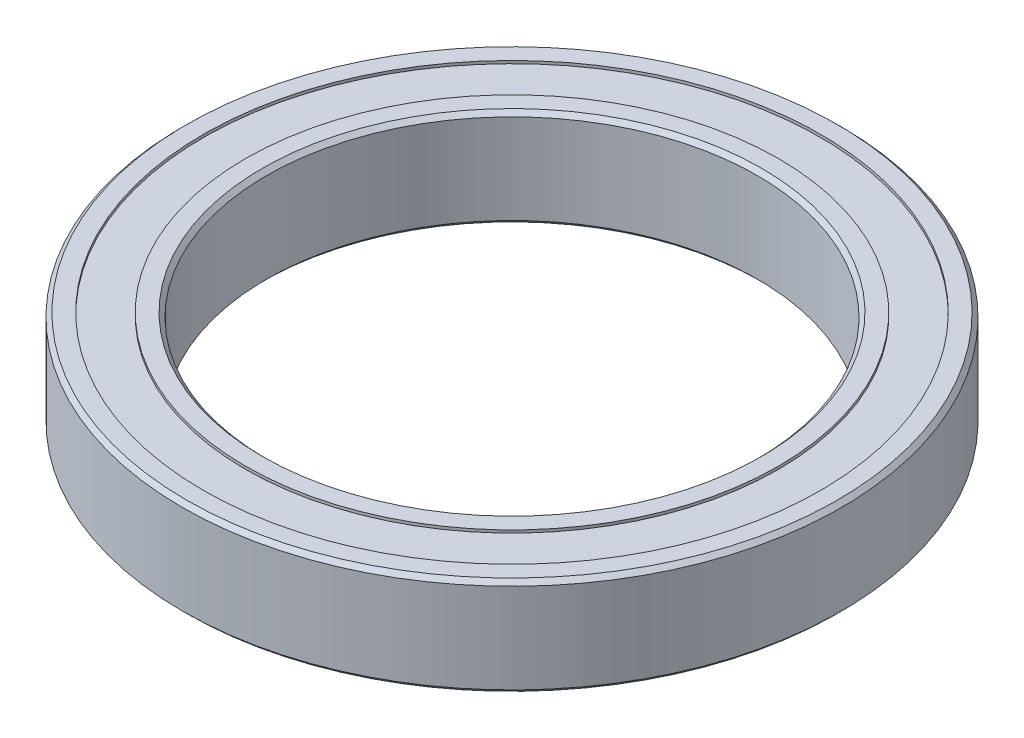
SolidWorks part; units mm, degrees
ref_plane "Front Plane" through (0, 0, 0) normal (0, 0, 1) x (1, 0, 0)
ref_plane "Top Plane" through (0, 0, 0) normal (0, 1, 0) x (1, 0, 0)
ref_plane "Right Plane" through (0, 0, 0) normal (1, 0, 0) x (0, 0, -1)
sketch "Sketch1" plane through (0, 0, 0) normal (0, 1, 0) x (1, 0, 0)
  circle A0 centre (0, 0) radius 17.5
  circle A1 centre (0, 0) radius 23.5
  dimension "D1" = 47
  dimension "D2" = 35
extrude "Boss-Extrude1" add sketch "Sketch1" along normal blind 7
sketch "Sketch2" plane through (0, 7, 0) normal (0, 1, 0) x (1, 0, 0)
  circle A2 centre (0, 0) radius 19
  circle A3 centre (0, 0) radius 19
  circle A5 centre (0, 0) radius 22
  circle A6 centre (0, 0) radius 22
  dimension "D1" = 1.5
  dimension "D2" = 1.5
extrude "Cut-Extrude1" cut sketch "Sketch2" against normal blind 0.2
chamfer "Chamfer1" distance 0.3 angle 45
sketch "Sketch3" plane through (0, 0, 0) normal (0, -1, 0) x (1, 0, 0)
  circle A0 centre (0, 0) radius 19 construction
  circle A1 centre (0, 0) radius 22
  circle A2 centre (0, 0) radius 22
  circle A3 centre (0, 0) radius 19
  dimension "D1" = 0
extrude "Cut-Extrude2" cut sketch "Sketch3" against normal blind 0.2
